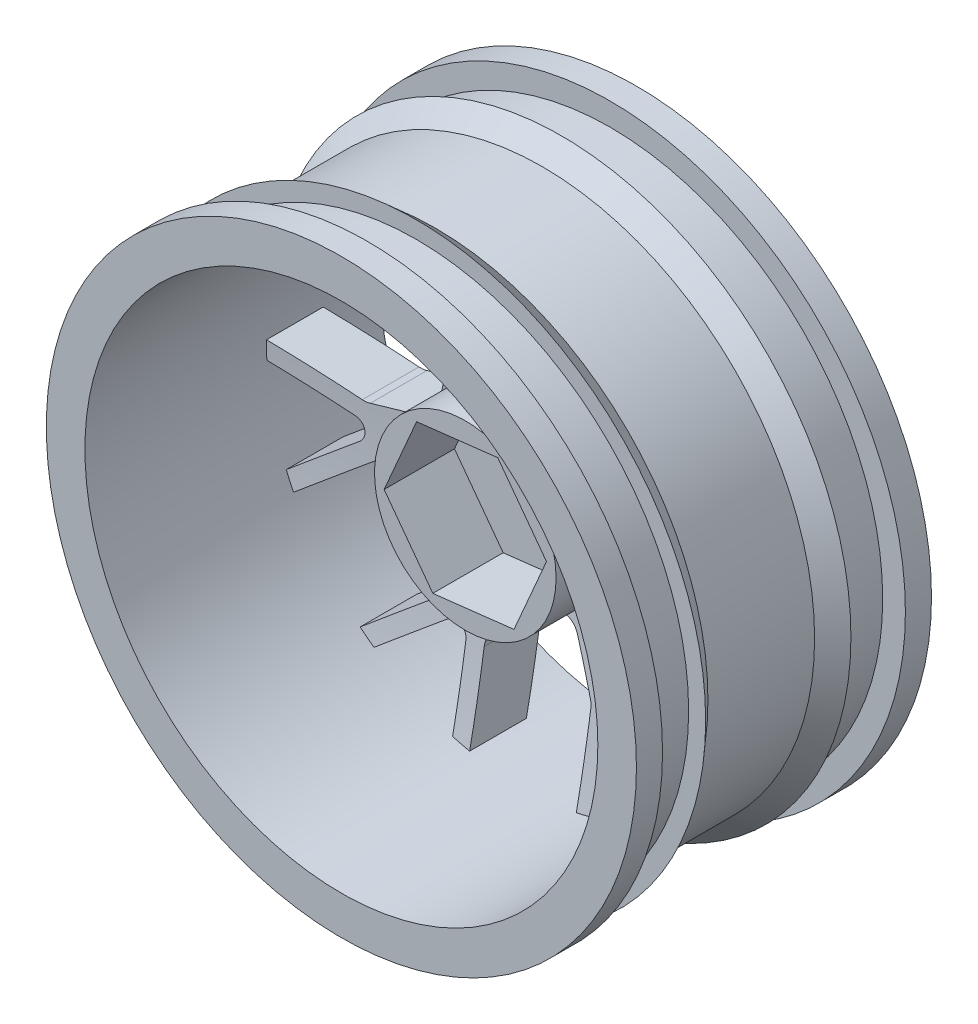
SolidWorks part; units mm, degrees
ref_plane "Front" through (0, 0, 0) normal (0, 0, 1) x (1, 0, 0)
ref_plane "Top" through (0, 0, 0) normal (0, 1, 0) x (1, 0, 0)
ref_plane "Right" through (0, 0, 0) normal (1, 0, 0) x (0, 0, -1)
sketch "Sketch4" plane through (0, 0, 0) normal (1, 0, 0) x (0, 0, -1)
  line L0 (0, 0) -> (26, 0) construction
  line L1 (0, 22.6) -> (0, 26)
  line L2 (0, 26) -> (2.3, 26)
  line L3 (2.3, 26) -> (2.3, 24)
  line L4 (2.3, 24) -> (6.6, 24)
  line L5 (6.6, 24) -> (6.6, 25.5)
  line L6 (6.6, 25.5) -> (8.3, 24)
  line L7 (8.3, 24) -> (17.7, 24)
  line L8 (13, 24) -> (13, 26) construction
  line L9 (0, 22.6) -> (26, 22.6)
  line L11 (26, 22.6) -> (26, 26)
  line L12 (26, 26) -> (23.7, 26)
  line L13 (23.7, 26) -> (23.7, 24)
  line L14 (23.7, 24) -> (19.4, 24)
  line L15 (19.4, 24) -> (19.4, 25.5)
  line L16 (19.4, 25.5) -> (17.7, 24)
  dimension "D1" = 3.4
  dimension "D2" = 2.3
  dimension "D3" = 4.3
  dimension "D4" = 4.7
  dimension "D5" = 2
  dimension "D6" = 26
  dimension "D7" = 1.7
  dimension "D8" = 1.5
revolve "Revolve1" add sketch "Sketch4" angle 360 about L0
sketch "Sketch6" plane through (0, 0, 0) normal (1, 0, 0) x (0, 0, -1)
  line L0 (0, 0) -> (26, 0) construction
  line L1 (26, -22.6) -> (26, 22.6) construction
  line L2 (0, 26) -> (26, 26) construction
  line L3 (26, -26) -> (26, 26) construction
  line L4 (13, 0) -> (13, 26) construction
  line L5 (18.5, -22.6) -> (18.5, -15.9253) construction
  line L6 (26, -26) -> (0, -26) construction
  line L7 (23.7, 24) -> (23.7, -24) construction
  line L8 (23.7, 0) -> (18.7, 0)
  line L9 (13, 0) -> (13, -26) construction
  line L10 (16, -22.6) -> (21, -22.6)
  spline S0 degree 2 poles (21, -22.6) (23.3323, -11.4217) (23.7, 0) knots 0 0 0 1 1 1
  spline S1 degree 2 poles (16, -22.6) (18.3323, -11.4217) (18.7, 0) knots 0 0 0 1 1 1
  point P22 (23.7, 0)
  point P30 (18.7, 0)
  dimension "D1" = 3.4
  dimension "D2" = 5
  dimension "D3" = 5
  dimension "D4" = 1.7
  dimension "D5" = 10.1
  dimension "D6" = 12.5
  dimension "D7" = 1.7
  dimension "D8" = 5
revolve "Revolve2" add sketch "Sketch6" angle 360 about L0
sketch "Sketch7" plane through (0, 0, -26) normal (0, 0, -1) x (-1, 0, 0)
  line L0 (1.5212, -9.45) -> (-1.5212, -9.45)
  line L1 (-4.7, -14.7654) -> (-4.7, -22.1059)
  line L2 (0, -9.45) -> (0, -13.85) construction
  line L3 (-2.8942, -10.3459) -> (-4.573, -14.1613)
  line L4 (2.8942, -10.3459) -> (4.573, -14.1613)
  line L5 (4.7, -14.7654) -> (4.7, -22.1059)
  line L6 (-8.6137, -12.8807) -> (-14.3527, -17.4574)
  line L7 (-6.2842, -8.7133) -> (-8.2205, -12.4047)
  line L8 (-6.4398, -7.0813) -> (-8.3368, -4.7026)
  line L9 (-9.8932, -4.1878) -> (-13.923, -5.2541)
  line L10 (-14.4745, -5.5315) -> (-20.2135, -10.1082)
  line L11 (-15.4411, -1.2965) -> (-22.5975, 0.3369)
  line L12 (-10.7305, -0.5195) -> (-14.8238, -1.3071)
  line L13 (-9.5516, 0.6197) -> (-8.8746, 3.5859)
  line L14 (-9.4425, 5.1238) -> (-12.7887, 7.6095)
  line L15 (-13.3494, 7.8678) -> (-20.5058, 9.5012)
  line L16 (-10.641, 11.2639) -> (-13.8259, 17.8775)
  line L17 (-7.0965, 8.0656) -> (-10.2645, 10.7748)
  line L18 (-5.4708, 7.8541) -> (-2.7296, 9.1742)
  line L19 (-1.8813, 10.5771) -> (-2.0243, 14.743)
  line L20 (-2.1719, 15.3424) -> (-5.3568, 21.956)
  line L21 (2.1719, 15.3424) -> (5.3568, 21.956)
  line L22 (1.8813, 10.5771) -> (2.0243, 14.743)
  line L23 (2.7296, 9.1742) -> (5.4708, 7.8541)
  line L24 (7.0965, 8.0656) -> (10.2645, 10.7748)
  line L25 (10.641, 11.2639) -> (13.8259, 17.8775)
  line L26 (13.3494, 7.8678) -> (20.5058, 9.5012)
  line L27 (9.4425, 5.1238) -> (12.7887, 7.6095)
  line L28 (8.8746, 3.5859) -> (9.5516, 0.6197)
  line L29 (10.7305, -0.5195) -> (14.8238, -1.3071)
  line L30 (15.4411, -1.2965) -> (22.5975, 0.3369)
  line L31 (14.4745, -5.5315) -> (20.2135, -10.1082)
  line L32 (9.8932, -4.1878) -> (13.923, -5.2541)
  line L33 (8.3368, -4.7026) -> (6.4398, -7.0813)
  line L34 (6.2842, -8.7133) -> (8.2205, -12.4047)
  line L35 (8.6137, -12.8807) -> (14.3527, -17.4574)
  line L36 (6.2, -21.7329) -> (6.2, -14.951)
  line L37 (7.8235, -14.1691) -> (13.1258, -18.3976)
  line L38 (-13.1258, -18.3976) -> (-7.8235, -14.1691)
  line L39 (-6.2, -14.951) -> (-6.2, -21.7329)
  line L40 (-22.5677, -1.2085) -> (-15.9557, -2.7177)
  line L41 (-15.5548, -4.4744) -> (-20.8571, -8.7029)
  line L42 (-15.0156, 16.8906) -> (-12.073, 10.7803)
  line L43 (-13.1965, 9.3715) -> (-19.8084, 10.8806)
  line L44 (3.8436, 22.2708) -> (0.901, 16.1604)
  line L45 (-0.901, 16.1604) -> (-3.8436, 22.2708)
  line L46 (19.8084, 10.8806) -> (13.1965, 9.3715)
  line L47 (12.073, 10.7803) -> (15.0156, 16.8906)
  line L48 (20.8571, -8.7029) -> (15.5548, -4.4744)
  line L49 (15.9557, -2.7177) -> (22.5677, -1.2085)
  circle A0 centre (0, 0) radius 2.25
  circle A1 centre (0, 0) radius 22.6 construction
  arc A2 (-4.7, -22.1059) -> (4.7, -22.1059) centre (0, 0) ccw
  arc A3 (-20.2135, -10.1082) -> (-14.3527, -17.4574) centre (0, 0) ccw
  arc A4 (-20.5058, 9.5012) -> (-22.5975, 0.3369) centre (0, 0) ccw
  arc A5 (-5.3568, 21.956) -> (-13.8259, 17.8775) centre (0, 0) ccw
  arc A6 (13.8259, 17.8775) -> (5.3568, 21.956) centre (0, 0) ccw
  arc A7 (22.5975, 0.3369) -> (20.5058, 9.5012) centre (0, 0) ccw
  arc A8 (14.3527, -17.4574) -> (20.2135, -10.1082) centre (0, 0) ccw
  circle A9 centre (0, 0) radius 22.6 construction
  arc A10 (-4.7, -22.1059) -> (4.7, -22.1059) centre (0, 0) ccw
  arc A11 (6.2, -14.951) -> (7.8235, -14.1691) centre (7.2, -14.951) cw
  arc A12 (22.5975, 0.3369) -> (20.5058, 9.5012) centre (0, 0) ccw
  arc A13 (13.8259, 17.8775) -> (5.3568, 21.956) centre (0, 0) ccw
  arc A14 (-5.3568, 21.956) -> (-13.8259, 17.8775) centre (0, 0) ccw
  arc A15 (-20.5058, 9.5012) -> (-22.5975, 0.3369) centre (0, 0) ccw
  arc A16 (-20.2135, -10.1082) -> (-14.3527, -17.4574) centre (0, 0) ccw
  arc A17 (6.2, -21.7329) -> (13.1258, -18.3976) centre (0, 0) ccw
  arc A18 (14.3527, -17.4574) -> (20.2135, -10.1082) centre (0, 0) ccw
  arc A19 (-7.8235, -14.1691) -> (-6.2, -14.951) centre (-7.2, -14.951) cw
  arc A20 (-13.1258, -18.3976) -> (-6.2, -21.7329) centre (0, 0) ccw
  arc A21 (-15.9557, -2.7177) -> (-15.5548, -4.4744) centre (-16.1783, -3.6926) cw
  arc A22 (-22.5677, -1.2085) -> (-20.8571, -8.7029) centre (0, 0) ccw
  arc A23 (-12.073, 10.7803) -> (-13.1965, 9.3715) centre (-12.974, 10.3464) cw
  arc A24 (-15.0156, 16.8906) -> (-19.8084, 10.8806) centre (0, 0) ccw
  arc A25 (0.901, 16.1604) -> (-0.901, 16.1604) centre (0, 16.5943) cw
  arc A26 (3.8436, 22.2708) -> (-3.8436, 22.2708) centre (0, 0) ccw
  arc A27 (13.1965, 9.3715) -> (12.073, 10.7803) centre (12.974, 10.3464) cw
  arc A28 (19.8084, 10.8806) -> (15.0156, 16.8906) centre (0, 0) ccw
  arc A29 (15.5548, -4.4744) -> (15.9557, -2.7177) centre (16.1783, -3.6926) cw
  arc A30 (20.8571, -8.7029) -> (22.5677, -1.2085) centre (0, 0) ccw
  arc A31 (8.2205, -12.4047) -> (8.6137, -12.8807) centre (9.5489, -11.7079) ccw
  arc A32 (6.4398, -7.0813) -> (6.2842, -8.7133) centre (7.6126, -8.0166) ccw
  arc A33 (9.8932, -4.1878) -> (8.3368, -4.7026) centre (9.5095, -5.6379) ccw
  arc A34 (14.4745, -5.5315) -> (13.923, -5.2541) centre (13.5392, -6.7042) ccw
  arc A35 (14.8238, -1.3071) -> (15.4411, -1.2965) centre (15.1073, 0.1658) ccw
  arc A36 (9.5516, 0.6197) -> (10.7305, -0.5195) centre (11.014, 0.9535) ccw
  arc A37 (9.4425, 5.1238) -> (8.8746, 3.5859) centre (10.337, 3.9197) ccw
  arc A38 (13.3494, 7.8678) -> (12.7887, 7.6095) centre (13.6831, 6.4054) ccw
  arc A39 (1.8813, 10.5771) -> (2.7296, 9.1742) centre (3.3805, 10.5256) ccw
  arc A40 (5.4708, 7.8541) -> (7.0965, 8.0656) centre (6.1216, 9.2056) ccw
  arc A41 (10.2645, 10.7748) -> (10.641, 11.2639) centre (9.2896, 11.9147) ccw
  arc A42 (2.1719, 15.3424) -> (2.0243, 14.743) centre (3.5234, 14.6916) ccw
  arc A43 (-10.641, 11.2639) -> (-10.2645, 10.7748) centre (-9.2896, 11.9147) ccw
  arc A44 (-7.0965, 8.0656) -> (-5.4708, 7.8541) centre (-6.1216, 9.2056) ccw
  arc A45 (-2.7296, 9.1742) -> (-1.8813, 10.5771) centre (-3.3805, 10.5256) ccw
  arc A46 (-2.0243, 14.743) -> (-2.1719, 15.3424) centre (-3.5234, 14.6916) ccw
  arc A47 (-12.7887, 7.6095) -> (-13.3494, 7.8678) centre (-13.6831, 6.4054) ccw
  arc A48 (-8.8746, 3.5859) -> (-9.4425, 5.1238) centre (-10.337, 3.9197) ccw
  arc A49 (-15.4411, -1.2965) -> (-14.8238, -1.3071) centre (-15.1073, 0.1658) ccw
  arc A50 (-10.7305, -0.5195) -> (-9.5516, 0.6197) centre (-11.014, 0.9535) ccw
  arc A51 (-6.2842, -8.7133) -> (-6.4398, -7.0813) centre (-7.6126, -8.0166) ccw
  arc A52 (-8.3368, -4.7026) -> (-9.8932, -4.1878) centre (-9.5095, -5.6379) ccw
  arc A53 (-13.923, -5.2541) -> (-14.4745, -5.5315) centre (-13.5392, -6.7042) ccw
  arc A54 (-8.6137, -12.8807) -> (-8.2205, -12.4047) centre (-9.5489, -11.7079) ccw
  arc A55 (-4.7, -14.7654) -> (-4.573, -14.1613) centre (-3.2, -14.7654) cw
  arc A56 (4.573, -14.1613) -> (4.7, -14.7654) centre (3.2, -14.7654) cw
  arc A57 (-1.5212, -9.45) -> (-2.8942, -10.3459) centre (-1.5212, -10.95) ccw
  arc A58 (1.5212, -9.45) -> (2.8942, -10.3459) centre (1.5212, -10.95) cw
  point P3 (-2.25, 0)
  point P4 (0, 2.25)
  point P5 (2.25, 0)
  point P6 (0, -2.25)
  point P10 (0, -9.45)
  point P141 (-4.7, -14.45)
  point P144 (4.7, -14.45)
  point P147 (-2.5, -9.45)
  point P150 (2.5, -9.45)
  dimension "D1" = 4.5
  dimension "D9" = 1
  dimension "D11" = 1.5
  dimension "D2" = 5
  dimension "D3" = 7.2
  dimension "D4" = 2.2
  dimension "D5" = 5
  dimension "D7" = 1.5
  dimension "D8" = 1.5
  dimension "D6" = 7
  dimension "D10" = 7
extrude "Cut-Extrude1" cut sketch "Sketch7" against normal through all both and the other way through all
ref_plane "Plane1" through (0, 0, -23.7) normal (0, 0, -1) x (-1, 0, 0)
sketch "Sketch8" plane through (0, 0, -23.7) normal (0, 0, -1) x (-1, 0, 0)
  circle A0 centre (0, 0) radius 8
  dimension "D1" = 16
extrude "Cut-Extrude2" cut sketch "Sketch8" against normal blind 3
sketch "Sketch9" plane through (0, 0, -20.7) normal (0, 0, -1) x (-1, 0, 0)
  line L1 (4.2904, 5.7821) -> (-2.8623, 6.6066)
  line L2 (-2.8623, 6.6066) -> (-7.1526, 0.8245)
  line L3 (-7.1526, 0.8245) -> (-4.2904, -5.7821)
  line L4 (-4.2904, -5.7821) -> (2.8623, -6.6066)
  line L5 (2.8623, -6.6066) -> (7.1526, -0.8245)
  line L6 (7.1526, -0.8245) -> (4.2904, 5.7821)
  circle A0 centre (0, 0) radius 6.2354 construction
  circle A1 centre (0, 0) radius 8
  circle A4 centre (0, 0) radius 8
  dimension "D2" = 7.2
  dimension "D1" = 0
extrude "Boss-Extrude1" add sketch "Sketch9" against normal blind 8.6291
sketch "Sketch10" plane through (0, 0, -20.7) normal (0, 0, -1) x (-1, 0, 0)
  circle A0 centre (0, 0) radius 8 construction
  circle A1 centre (0, 0) radius 8
  circle A2 centre (0, 0) radius 6
  circle A3 centre (0, 0) radius 6 construction
  dimension "D1" = 2
extrude "Boss-Extrude2" add sketch "Sketch10" along normal blind 0.8
sketch "Sketch11" plane through (0, 0, -21.5) normal (0, 0, -1) x (-1, 0, 0)
  line L0 (0, 0) -> (8, 0) construction
  circle A0 centre (0, 0) radius 8 construction
  arc A5 (5.8462, -1.35) -> (5.8462, 1.35) centre (6.5, 0) ccw
  circle A14 centre (0, 0) radius 6 construction
  arc A15 (5.8462, -1.35) -> (5.8462, 1.35) centre (0, 0) ccw
  arc A16 (0.5226, -5.9772) -> (3.0905, -5.1429) centre (0, 0) ccw
  arc A17 (0.5226, -5.9772) -> (3.0905, -5.1429) centre (2.0086, -6.1819) ccw
  arc A18 (-5.5231, -2.3441) -> (-3.9361, -4.5285) centre (0, 0) ccw
  arc A19 (-5.5231, -2.3441) -> (-3.9361, -4.5285) centre (-5.2586, -3.8206) ccw
  arc A20 (-3.9361, 4.5285) -> (-5.5231, 2.3441) centre (0, 0) ccw
  arc A21 (-3.9361, 4.5285) -> (-5.5231, 2.3441) centre (-5.2586, 3.8206) ccw
  arc A22 (3.0905, 5.1429) -> (0.5226, 5.9772) centre (0, 0) ccw
  arc A23 (3.0905, 5.1429) -> (0.5226, 5.9772) centre (2.0086, 6.1819) ccw
  dimension "D1" = 3
  dimension "D2" = 5
extrude "Cut-Extrude3" cut sketch "Sketch11" against normal up to surface (0.8 mm away) up to face at (-6, 0, -20.7)
sketch "Sketch13" plane through (0, 0, -20.7) normal (0, 0, -1) x (-1, 0, 0)
  circle A0 centre (0, 0) radius 2.25
  dimension "D1" = 4.5
extrude "Cut-Extrude4" cut sketch "Sketch13" against normal through all both and the other way through all
ref_plane "Plane2" through (0, 0, -18.2709) normal (0, 0, 1) x (1, 0, 0)
sketch "Sketch14" plane through (0, 0, -18.2709) normal (0, 0, 1) x (1, 0, 0)
  line L6 (2.8623, 6.6066) -> (-4.2904, 5.7821)
  line L7 (-4.2904, 5.7821) -> (-7.1526, -0.8245)
  line L8 (-7.1526, -0.8245) -> (-2.8623, -6.6066)
  line L9 (-2.8623, -6.6066) -> (4.2904, -5.7821)
  line L10 (4.2904, -5.7821) -> (7.1526, 0.8245)
  line L11 (7.1526, 0.8245) -> (2.8623, 6.6066)
  line L12 (2.8623, 6.6066) -> (-4.2904, 5.7821)
  line L13 (-4.2904, 5.7821) -> (-7.1526, -0.8245)
  line L14 (-7.1526, -0.8245) -> (-2.8623, -6.6066)
  line L15 (-2.8623, -6.6066) -> (4.2904, -5.7821)
  line L16 (4.2904, -5.7821) -> (7.1526, 0.8245)
  line L17 (7.1526, 0.8245) -> (2.8623, 6.6066)
  circle A0 centre (0, 0) radius 2.25 construction
  circle A1 centre (0, 0) radius 2.25
  dimension "D1" = 0
extrude "Boss-Extrude3" add sketch "Sketch14" against normal up to surface up to face at (0, -2.25, -18.6084)
sketch "Sketch15" plane through (0, 0, -18.2709) normal (0, 0, 1) x (1, 0, 0)
  line L6 (-4.2904, 5.7821) -> (-7.1526, -0.8245)
  line L7 (-7.1526, -0.8245) -> (-2.8623, -6.6066)
  line L8 (-2.8623, -6.6066) -> (4.2904, -5.7821)
  line L9 (4.2904, -5.7821) -> (7.1526, 0.8245)
  line L10 (7.1526, 0.8245) -> (2.8623, 6.6066)
  line L11 (2.8623, 6.6066) -> (-4.2904, 5.7821)
  line L12 (-4.2904, 5.7821) -> (-7.1526, -0.8245)
  line L13 (-7.1526, -0.8245) -> (-2.8623, -6.6066)
  line L14 (-2.8623, -6.6066) -> (4.2904, -5.7821)
  line L15 (4.2904, -5.7821) -> (7.1526, 0.8245)
  line L16 (7.1526, 0.8245) -> (2.8623, 6.6066)
  line L17 (2.8623, 6.6066) -> (-4.2904, 5.7821)
  circle A0 centre (0, 0) radius 2.25 construction
  circle A1 centre (0, 0) radius 2.25
  dimension "D1" = 0
extrude "Boss-Extrude4" add sketch "Sketch15" along normal blind 1.1509
sketch "Sketch16" plane through (0, 0, -12.0709) normal (0, 0, 1) x (1, 0, 0)
  line L6 (2.8623, 6.6066) -> (-4.2904, 5.7821)
  line L7 (-4.2904, 5.7821) -> (-7.1526, -0.8245)
  line L8 (-7.1526, -0.8245) -> (-2.8623, -6.6066)
  line L9 (-2.8623, -6.6066) -> (4.2904, -5.7821)
  line L10 (4.2904, -5.7821) -> (7.1526, 0.8245)
  line L11 (7.1526, 0.8245) -> (2.8623, 6.6066)
  line L12 (2.8623, 6.6066) -> (-4.2904, 5.7821)
  line L13 (-4.2904, 5.7821) -> (-7.1526, -0.8245)
  line L14 (-7.1526, -0.8245) -> (-2.8623, -6.6066)
  line L15 (-2.8623, -6.6066) -> (4.2904, -5.7821)
  line L16 (4.2904, -5.7821) -> (7.1526, 0.8245)
  line L17 (7.1526, 0.8245) -> (2.8623, 6.6066)
  circle A1 centre (0, 0) radius 2.25 construction
  circle A2 centre (0, 0) radius 8
  circle A4 centre (0, 0) radius 8
  circle A5 centre (0, 0) radius 2.25
  line M9 (-2.8623, -6.6066) -> (-7.1526, -0.8245)
  line M10 (-7.1526, -0.8245) -> (-4.2904, 5.7821)
  line M11 (-4.2904, 5.7821) -> (2.8623, 6.6066)
  line M12 (2.8623, 6.6066) -> (7.1526, 0.8245)
  line M13 (7.1526, 0.8245) -> (4.2904, -5.7821)
  line M14 (4.2904, -5.7821) -> (-2.8623, -6.6066)
  circle M15 centre (0, 0) radius 8
  dimension "D1" = 0
  dimension "D2" = 0
extrude "Boss-Extrude5" add sketch "Sketch16" along normal blind 1.1509 contours M15 M14 M9 M10 M11 M12 M13
